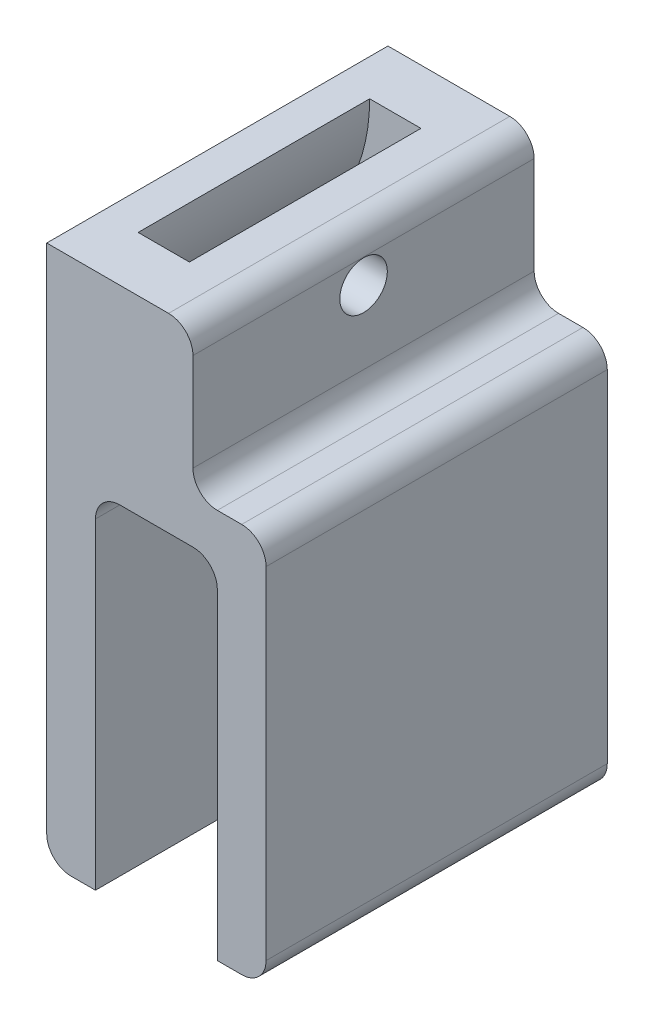
SolidWorks part; units mm, degrees
ref_plane "前视基准面" through (0, 0, 0) normal (0, 0, 1) x (1, 0, 0)
ref_plane "上视基准面" through (0, 0, 0) normal (0, 1, 0) x (1, 0, 0)
ref_plane "右视基准面" through (0, 0, 0) normal (1, 0, 0) x (0, 0, -1)
other "Configuration Table"
sketch "Sketch4" plane through (0, 0, 0) normal (0, 0, 1) x (1, 0, 0)
  line L0 (7, -16) -> (8, -16)
  line L1 (7, 0) -> (8, 0)
  line L2 (0, 0) -> (0, -15)
  line L3 (1, -16) -> (2, -16)
  line L4 (9, -1) -> (9, -15)
  line L6 (2, -16) -> (2, -2.8068)
  line L7 (3, -1.8068) -> (6, -1.8068)
  line L8 (7, -16) -> (7, -2.8068)
  line L11 (0, 0) -> (0, 6)
  line L12 (0, 6) -> (5, 6)
  line L13 (6, 1) -> (6, 5)
  arc A0 (0, -15) -> (1, -16) centre (1, -15) ccw
  arc A1 (8, -16) -> (9, -15) centre (8, -15) ccw
  arc A2 (6, -1.8068) -> (7, -2.8068) centre (6, -2.8068) cw
  arc A3 (2, -2.8068) -> (3, -1.8068) centre (3, -2.8068) cw
  arc A4 (8, 0) -> (9, -1) centre (8, -1) cw
  arc A5 (7, 0) -> (6, 1) centre (7, 1) cw
  arc A6 (5, 6) -> (6, 5) centre (5, 5) cw
  point P16 (9, -16)
  point P19 (7, -1.8068)
  point P22 (2, -1.8068)
  point P25 (9, 0)
  point P28 (6, 0)
  point P31 (6, 6)
  dimension "D7" = 1
  dimension "D1" = 9
  dimension "D2" = 5
  dimension "D3" = 2
  dimension "D4" = 16
  dimension "D5" = 6
  dimension "D6" = 6
extrude "Boss-Extrude3" add sketch "Sketch4" along normal blind 14
sketch "Sketch5" plane through (0, 0, 0) normal (-1, 0, 0) x (0, 0, 1)
  line L0 (0, 0) -> (14, 0)
  line L1 (14, 6) -> (14, -15) construction
  line L3 (2.25, 1.5) -> (11.75, 1.5)
  line L4 (2.25, 1.5) -> (2.25, -1.5)
  line L5 (2.25, -1.5) -> (11.75, -1.5)
  line L6 (11.75, 1.5) -> (11.75, -1.5)
  line L7 (2.25, 1.5) -> (11.75, -1.5) construction
  line L8 (2.25, -1.5) -> (11.75, 1.5) construction
  point P5 (7, 0)
  dimension "D1" = 3
  dimension "D2" = 9.5
sketch "Sketch8" plane through (0, 0, 14) normal (0, 0, 1) x (1, 0, 0)
  line L0 (0, 6) -> (-6, 6)
  circle A0 centre (-6, 6) radius 11
  circle A1 centre (-6, 6) radius 8.6
  dimension "D2" = 2.4
  dimension "D1" = 6
sweep "Cut-Sweep2" cut profiles "Sketch5" path "Sketch8"
sketch "Sketch9" plane through (6, 0, 0) normal (1, 0, 0) x (0, 0, -1)
  line L0 (-14, 5) -> (0, 5)
  line L1 (-7, 5) -> (-7, 4)
  circle A0 centre (-7, 4) radius 0.975
  dimension "D1" = 1.95
  dimension "D2" = 1
extrude "Cut-Extrude1" cut sketch "Sketch9" against normal blind 4.5 contours A0
sketch "Sketch11" plane through (0, 0, 0) normal (-1, 0, 0) x (0, 0, 1)
  line L0 (11.75, 1.5) -> (11.75, -1.5) construction
  line L2 (2.25, -1.5) -> (2.25, 0)
  line L3 (2.25, 0) -> (11.75, 0)
  line L4 (11.75, -1.5) -> (11.75, 0)
  line L5 (14, -16) -> (0, -16) construction
  line L7 (2.25, -1.5) -> (2.25, -16)
  line L8 (2.25, -16) -> (11.75, -16)
  line L9 (11.75, -1.5) -> (11.75, -16)
extrude "Cut-Extrude3" cut sketch "Sketch11" against normal blind 1
fillet "Fillet2" radius 4 1 edges at (1, -0.5765, 7)
